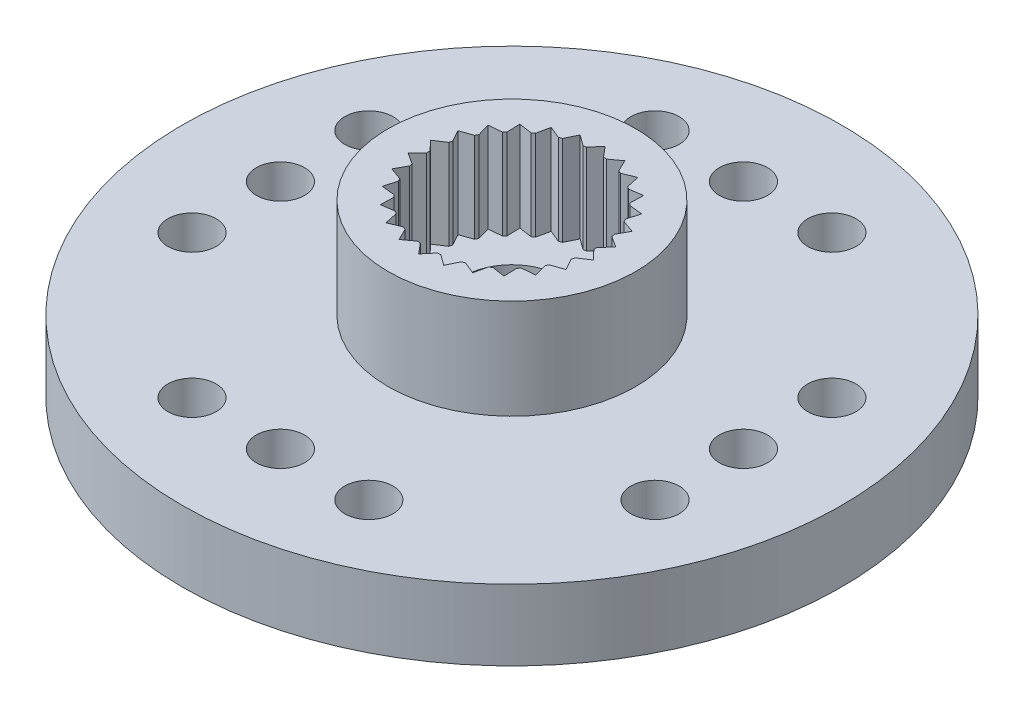
SolidWorks part; units mm, degrees
ref_plane "Спереди" through (0, 0, 0) normal (0, 0, 1) x (1, 0, 0)
ref_plane "Сверху" through (0, 0, 0) normal (0, 1, 0) x (1, 0, 0)
ref_plane "Справа" through (0, 0, 0) normal (1, 0, 0) x (0, 0, -1)
sketch "Эскиз1" plane through (0, 0, 0) normal (0, 1, 0) x (1, 0, 0)
  circle A0 centre (0, 0) radius 10.25
  dimension "D1" = 20.5
extrude "Бобышка-Вытянуть1" add sketch "Эскиз1" along normal blind 2.2
sketch "Эскиз2" plane through (0, 2.2, 0) normal (0, 1, 0) x (1, 0, 0)
  circle A0 centre (0, 0) radius 3.85
  circle A1 centre (0, 0) radius 2.6
  dimension "D1" = 7.7
  dimension "D2" = 5.2
extrude "Бобышка-Вытянуть2" add sketch "Эскиз2" along normal blind 3.1
sketch "Эскиз3" plane through (0, 2.2, 0) normal (0, 1, 0) x (1, 0, 0)
  line L0 (0, 10.25) -> (0, -10.25) construction
  line L1 (-10.25, 0) -> (10.25, 0) construction
  circle A0 centre (0, 0) radius 10.25 construction
  circle A1 centre (0, 7.2) radius 0.75
  circle A2 centre (7.2, 0) radius 0.75
  circle A3 centre (0, -7.2) radius 0.75
  circle A4 centre (-7.2, 0) radius 0.75
  circle A5 centre (0, 0) radius 1.5
  circle A6 centre (2.75, 7.2) radius 0.75
  circle A7 centre (2.75, -7.2) radius 0.75
  circle A8 centre (-2.75, 7.2) radius 0.75
  circle A9 centre (-2.75, -7.2) radius 0.75
  circle A10 centre (7.2, 2.75) radius 0.75
  circle A11 centre (-7.2, 2.75) radius 0.75
  circle A12 centre (7.2, -2.75) radius 0.75
  circle A13 centre (-7.2, -2.75) radius 0.75
  dimension "D1" = 1.5
  dimension "D2" = 3
  dimension "D7" = 3.05
  dimension "D8" = 3.05
  dimension "D9" = 3.05
  dimension "D10" = 3.05
  dimension "D11" = 14.4
  dimension "D3" = 2
  dimension "D4" = 2
  dimension "D5" = 2
  dimension "D6" = 2
extrude "Вырез-Вытянуть1" cut sketch "Эскиз3" against normal through all
sketch "Эскиз4" plane through (0, 0, 0) normal (0, -1, 0) x (1, 0, 0)
  circle A0 centre (0, 0) radius 4.25
  circle A1 centre (0, 0) radius 3.25
  circle A2 centre (0, 0) radius 3
  circle M10 centre (0, 0) radius 1.5
  dimension "D1" = 8.5
  dimension "D3" = 0.25
  dimension "D2" = 1
extrude "Вырез-Вытянуть2" cut sketch "Эскиз4" against normal blind 1 contours A0 A1 | A2 M10
sketch "Эскиз5" plane through (0, 2.2, 0) normal (0, 1, 0) x (1, 0, 0)
  circle A0 centre (0, 0) radius 1.5
  circle A1 centre (0, 0) radius 2.6
  circle A2 centre (0, 0) radius 2.6 construction
  circle A3 centre (0, 0) radius 1.5 construction
extrude "Бобышка-Вытянуть3" add sketch "Эскиз5" along normal blind 0.3
sketch "Эскиз6" plane through (0, 5.3, 0) normal (0, 1, 0) x (1, 0, 0)
  line L0 (0, 0) -> (0, 3.85) construction
  line L1 (0, 2.9) -> (-0.2629, 2.5867)
  line L2 (0, 2.9) -> (0.2629, 2.5867)
  line L3 (0, 2.6) -> (0, 2.9) construction
  arc A0 (-0.2629, 2.5867) -> (0.2629, 2.5867) centre (0, 0) cw
  circle A2 centre (0, 0) radius 3.85 construction
  dimension "D1" = 80
  dimension "D2" = 0.3
  dimension "D3" = 0.5258
extrude "Вырез-Вытянуть3" cut sketch "Эскиз6" against normal up to surface (2.8 mm away) up to face at (0, 2.5, 2.6)
pattern_circular "Круговой массив1" count 26 over 360 about axis through (0, 0, 0) along (0, 1, 0) of "Вырез-Вытянуть3"
